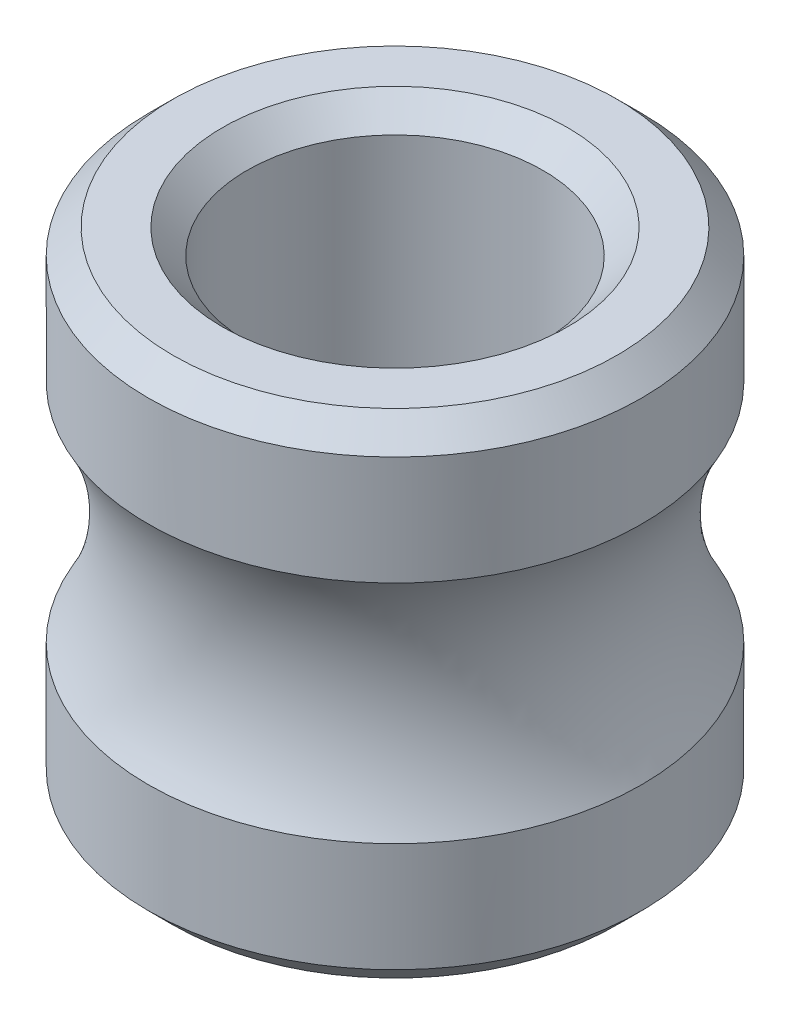
SolidWorks part; units mm, degrees
ref_plane "Front" through (0, 0, 0) normal (0, 0, 1) x (1, 0, 0)
ref_plane "Top" through (0, 0, 0) normal (0, 1, 0) x (1, 0, 0)
ref_plane "Right" through (0, 0, 0) normal (1, 0, 0) x (0, 0, -1)
sketch "Sketch1" plane through (0, 0, 0) normal (0, 1, 0) x (1, 0, 0)
  circle A2 centre (0, 0) radius 2
  circle A3 centre (0, 0) radius 1.2
extrude "Boss-Extrude1" add sketch "Sketch1" along normal mid plane 4
chamfer "Chamfer1" distance 0.2 angle 45 4 edges at (0, -2, 1.2) (0, -2, 2) (0, 2, 2) (0, 2, 1.2)
sketch "Sketch2" plane through (0, 0, 0) normal (1, 0, 0) x (0, 0, -1)
  circle A0 centre (3.55, 0) radius 1.8
  dimension "D1" = 3.55
sketch "Sketch3" plane through (0, 0, 0) normal (0, 1, 0) x (1, 0, 0)
  circle A0 centre (0, 0) radius 3.5532
sweep "Cut-Sweep1" cut profiles "Sketch2" path "Sketch3"
